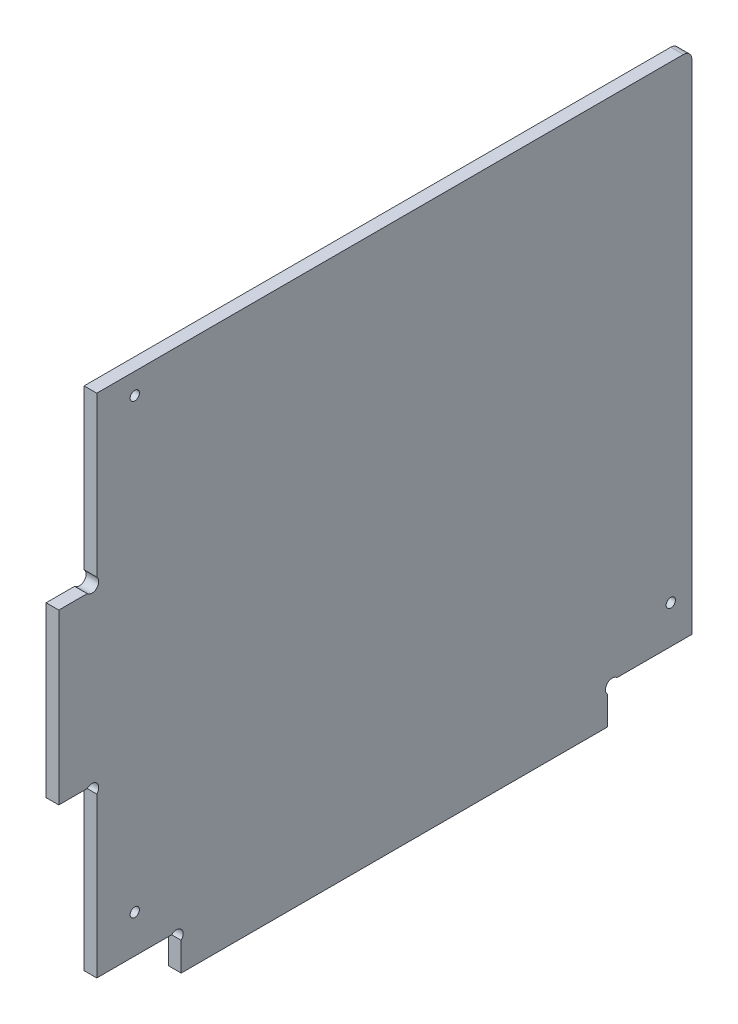
SolidWorks part; units mm, degrees
ref_plane "Plan de face" through (0, 0, 0) normal (0, 0, 1) x (1, 0, 0)
ref_plane "Plan de dessus" through (0, 0, 0) normal (0, 1, 0) x (1, 0, 0)
ref_plane "Plan de droite" through (0, 0, 0) normal (1, 0, 0) x (0, 0, -1)
sketch "Esquisse1" plane through (0, 0, 0) normal (1, 0, 0) x (0, 0, -1)
  line L11 (130, 6.7373) -> (130, 0)
  line L13 (29, 6.7373) -> (29, 0)
  line L14 (0, 49) -> (6.7373, 49)
  line L15 (0, 89) -> (6.7373, 89)
  line L16 (29, 0) -> (130, 0)
  line L17 (26.7373, 9) -> (9, 9)
  line L18 (9, 9) -> (9, 46.7373)
  line L19 (0, 49) -> (0, 89)
  line L20 (9, 91.2627) -> (9, 129)
  line L21 (9, 129) -> (150, 129)
  line L22 (150, 129) -> (150, 9)
  line L23 (150, 9) -> (132.2627, 9)
  arc A0 (132.2627, 9) -> (130, 6.7373) centre (131.1314, 7.8686) ccw
  arc A1 (9, 46.7373) -> (6.7373, 49) centre (7.8686, 47.8686) ccw
  arc A2 (26.7373, 9) -> (29, 6.7373) centre (27.8686, 7.8686) cw
  arc A3 (9, 91.2627) -> (6.7373, 89) centre (7.8686, 90.1314) cw
  dimension "D11" = 20
  dimension "D8" = 1.6
  dimension "D1" = 141
  dimension "D2" = 120
  dimension "D3" = 20
  dimension "D4" = 9
  dimension "D5" = 9
  dimension "D6" = 40
  dimension "D7" = 40
  dimension "D9" = 1.1314
  dimension "D10" = 2.2627
  dimension "D12" = 1.1314
  dimension "D13" = 2.2627
  dimension "D14" = 101
extrude "Extrusion1" add sketch "Esquisse1" along normal blind 3
sketch "Esquisse2" plane through (3, 0, 0) normal (1, 0, 0) x (0, 0, -1)
  line L0 (132.2627, 9) -> (150, 9) construction
  line L1 (150, 9) -> (150, 129) construction
  line L2 (9, 46.7373) -> (9, 9) construction
  line L3 (9, 9) -> (26.7373, 9) construction
  line L5 (150, 129) -> (9, 129) construction
  circle A1 centre (18, 124) radius 1.1
  circle A2 centre (18, 18) radius 1.1
  circle A3 centre (145, 18) radius 1.1
  dimension "D1" = 2.2
  dimension "D2" = 5
  dimension "D3" = 9
  dimension "D4" = 5
  dimension "D5" = 9
  dimension "D6" = 9
extrude "Enlèv. mat.-Extru.1" cut sketch "Esquisse2" against normal through all
fillet "Congé1" radius 2 1 edges at (1.5, 129, -150)
